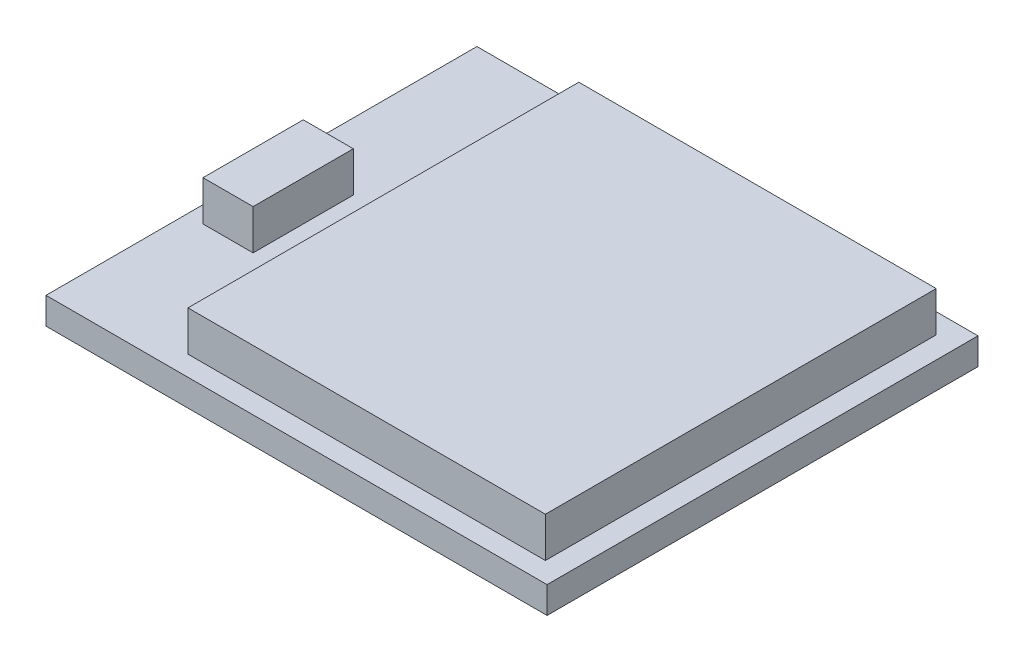
SolidWorks part; units mm, degrees
ref_plane "Front Plane" through (0, 0, 0) normal (0, 0, 1) x (1, 0, 0)
ref_plane "Top Plane" through (0, 0, 0) normal (0, 1, 0) x (1, 0, 0)
ref_plane "Right Plane" through (0, 0, 0) normal (1, 0, 0) x (0, 0, -1)
sketch "Sketch1" plane through (0, 0, 0) normal (0, 1, 0) x (1, 0, 0)
  line L1 (-7.5, 6.45) -> (7.5, 6.45)
  line L2 (-7.5, 6.45) -> (-7.5, -6.45)
  line L3 (-7.5, -6.45) -> (7.5, -6.45)
  line L4 (7.5, 6.45) -> (7.5, -6.45)
  line L5 (-7.5, 6.45) -> (7.5, -6.45) construction
  line L6 (-7.5, -6.45) -> (7.5, 6.45) construction
  point P0 (0, 0)
  dimension "D1" = 15
  dimension "D2" = 12.9
extrude "Boss-Extrude1" add sketch "Sketch1" along normal mid plane 0.8
sketch "Sketch2" plane through (0, 0.4, 0) normal (0, 1, 0) x (1, 0, 0)
  line L0 (1.5, 0) -> (0, 0) construction
  line L1 (-3.85, 5.85) -> (6.85, 5.85)
  line L2 (-3.85, 5.85) -> (-3.85, -5.85)
  line L3 (-3.85, -5.85) -> (6.85, -5.85)
  line L4 (6.85, 5.85) -> (6.85, -5.85)
  line L5 (-3.85, 5.85) -> (6.85, -5.85) construction
  line L6 (-3.85, -5.85) -> (6.85, 5.85) construction
  line L7 (7.5, -6.45) -> (7.5, 6.45) construction
  point P0 (1.5, 0)
  dimension "D1" = 11.7
  dimension "D2" = 10.7
  dimension "D3" = 0.65
extrude "Boss-Extrude2" add sketch "Sketch2" along normal offset from surface (1.2 mm away) 2 up to face at (0, -0.4, 0)
sketch "Sketch3" plane through (0, 0.4, 0) normal (0, 1, 0) x (1, 0, 0)
  line L0 (7.5, 6.45) -> (-7.5, 6.45) construction
  line L1 (-7, 0.75) -> (-5.5, 0.75)
  line L2 (-7, 0.75) -> (-7, -2.25)
  line L3 (-7, -2.25) -> (-5.5, -2.25)
  line L4 (-5.5, 0.75) -> (-5.5, -2.25)
  line L5 (-7, 0.75) -> (-5.5, -2.25) construction
  line L6 (-7, -2.25) -> (-5.5, 0.75) construction
  line L7 (-7.5, -6.45) -> (7.5, -6.45) construction
  line L9 (-7.5, 6.45) -> (-7.5, -6.45) construction
  point P0 (-6.25, -0.75)
  point P13 (-7.5, 0)
  dimension "D1" = 3
  dimension "D2" = 1.5
  dimension "D3" = 5.7
  dimension "D4" = 4.2
  dimension "D5" = 0.5
extrude "Boss-Extrude3" add sketch "Sketch3" along normal offset from surface (1.2 mm away) 2 up to face at (0, -0.4, 0)
